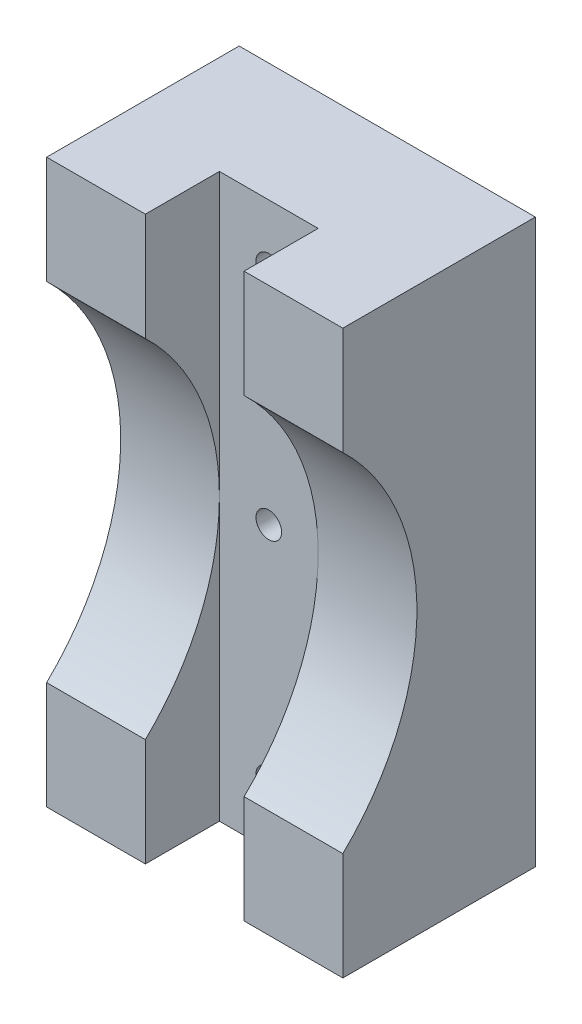
SolidWorks part; units mm, degrees
ref_plane "Front Plane" through (0, 0, 0) normal (0, 0, 1) x (1, 0, 0)
ref_plane "Top Plane" through (0, 0, 0) normal (0, 1, 0) x (1, 0, 0)
ref_plane "Right Plane" through (0, 0, 0) normal (1, 0, 0) x (0, 0, -1)
sketch "Sketch2" plane through (0, 0, 0) normal (1, 0, 0) x (0, 0, -1)
  line L0 (0, 22.5) -> (0, -22.5) construction
  line L1 (-7.5, 28.5) -> (-7.5, -28.5)
  line L2 (27, -28.5) -> (-27, -28.5)
  line L3 (27, -28.5) -> (27, 28.5)
  line L4 (27, 28.5) -> (-27, 28.5)
  line L5 (-27, -28.5) -> (-27, 28.5)
  line L6 (27, -28.5) -> (-27, 28.5) construction
  line L7 (27, 28.5) -> (-27, -28.5) construction
  line L8 (7.5, 28.5) -> (7.5, -28.5)
  line L9 (15, -28.5) -> (15, 28.5) construction
  circle A0 centre (0, 0) radius 15 construction
  circle A1 centre (0, 0) radius 22.5 construction
  arc A2 (0, 22.5) -> (0, -22.5) centre (9.375, 0) ccw
  arc A3 (0, 22.5) -> (0, -22.5) centre (-9.375, 0) cw
  point P16 (15, 0)
  dimension "D1" = 30
  dimension "D2" = 45
  dimension "D3" = 6
  dimension "D4" = 7.5
  dimension "D5" = 12
extrude "Boss-Extrude1" add sketch "Sketch2" along normal blind 10 contours L8 A3 L2 L3 L4
sketch "Sketch4" plane through (0, 0, 0) normal (-1, 0, 0) x (0, 0, 1)
  line L1 (-27, -28.5) -> (-15, -28.5)
  line L2 (-27, -28.5) -> (-27, 28.5)
  line L3 (-27, 28.5) -> (-15, 28.5)
  line L4 (-15, -28.5) -> (-15, 28.5)
  line L8 (-27, 28.5) -> (-7.5, 28.5) construction
  arc A0 (-7.5, 17.5891) -> (-7.5, -17.5891) centre (9.375, 0) ccw construction
  point P5 (0, 0)
  point P10 (0, 0)
extrude "Boss-Extrude2" add sketch "Sketch4" along normal blind 10
ref_plane "Plane1" through (-5, 0, 0) normal (-1, 0, 0) x (0, 0, 1)
mirror "Mirror1" about plane through (-5, 0, 0) normal (-1, 0, 0) of "Boss-Extrude1"
sketch "Sketch3" plane through (0, 0, -27) normal (0, 0, -1) x (-1, 0, 0)
  line L0 (5, 28.5) -> (5, -28.5) construction
  line L1 (-10, 28.5) -> (20, 28.5) construction
  line L2 (-10, -28.5) -> (20, -28.5) construction
  line L3 (0, 0) -> (-23.373, 0) construction
  line L4 (0, -28.5) -> (0, 28.5) construction
  circle A0 centre (5, -22.5) radius 1.3
  circle A1 centre (5, 22.5) radius 1.3
  circle A2 centre (5, 0) radius 1.3
  dimension "D1" = 2.6
  dimension "D3" = 2.6
  dimension "D2" = 6
extrude "Cut-Extrude1" cut sketch "Sketch3" against normal through all both and the other way through all
